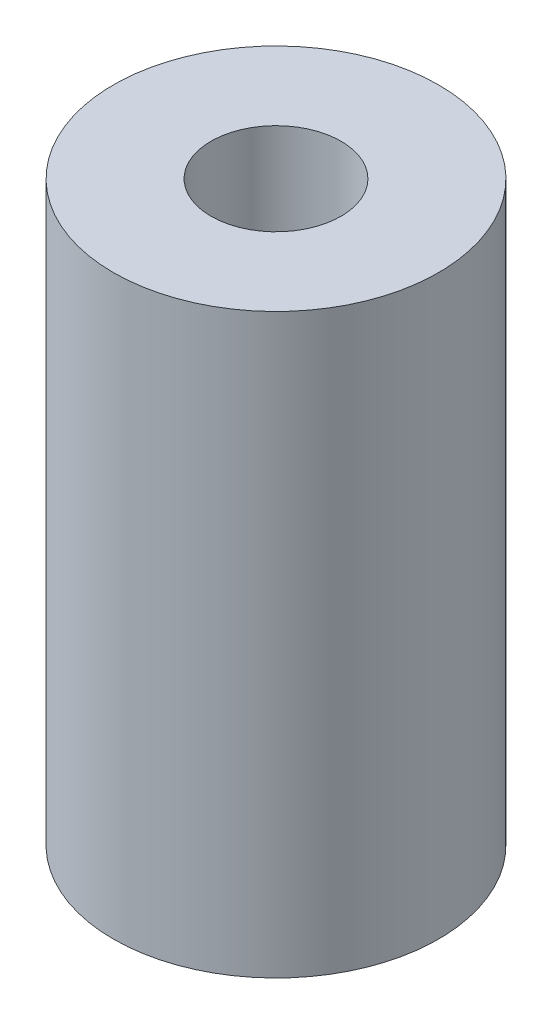
SolidWorks part; units mm, degrees
ref_plane "前视基准面" through (0, 0, 0) normal (0, 0, 1) x (1, 0, 0)
ref_plane "上视基准面" through (0, 0, 0) normal (0, 1, 0) x (1, 0, 0)
ref_plane "右视基准面" through (0, 0, 0) normal (1, 0, 0) x (0, 0, -1)
sketch "草图1" plane through (0, 0, 0) normal (0, 1, 0) x (1, 0, 0)
  circle A0 centre (0, 0) radius 1.6
  circle A1 centre (0, 0) radius 4
extrude "凸台-拉伸1" add sketch "草图1" along normal blind 14.2
